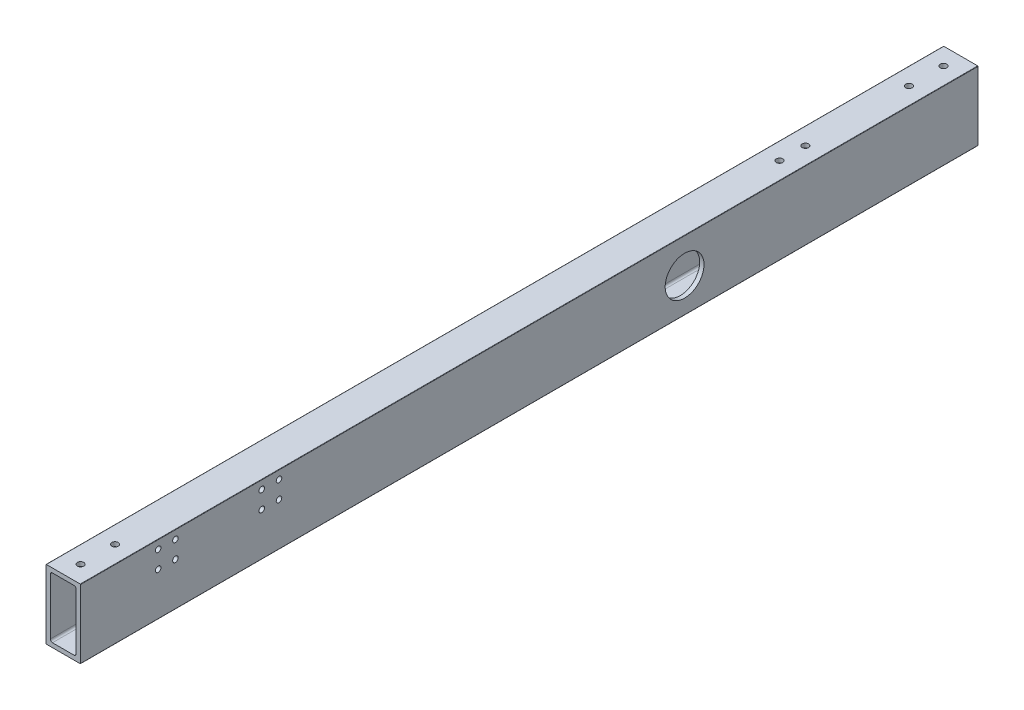
SolidWorks part; units mm, degrees
material "1060 Alloy"
ref_plane "Front Plane" through (0, 0, 0) normal (0, 0, 1) x (1, 0, 0)
ref_plane "Top Plane" through (0, 0, 0) normal (0, 1, 0) x (1, 0, 0)
ref_plane "Right Plane" through (0, 0, 0) normal (1, 0, 0) x (0, 0, -1)
ref_plane "Plane1" through (0, 0, 0) normal (0, 0, -1) x (-1, 0, 0)
sketch "Sketch1" plane through (0, 0, 0) normal (0, 0, -1) x (-1, 0, 0)
  line L0 (-3.175, 46.0375) -> (-3.175, 4.7625)
  line L1 (-4.7625, 3.175) -> (-20.6375, 3.175)
  line L2 (-22.225, 4.7625) -> (-22.225, 46.0375)
  line L3 (-20.6375, 47.625) -> (-4.7625, 47.625)
  line L4 (0, 0.254) -> (0, 50.546)
  line L5 (-0.254, 50.8) -> (-25.146, 50.8)
  line L6 (-25.4, 50.546) -> (-25.4, 0.254)
  line L7 (-25.146, 0) -> (-0.254, 0)
  arc A0 (-3.175, 4.7625) -> (-4.7625, 3.175) centre (-4.7625, 4.7625) cw
  arc A1 (-20.6375, 3.175) -> (-22.225, 4.7625) centre (-20.6375, 4.7625) cw
  arc A2 (-22.225, 46.0375) -> (-20.6375, 47.625) centre (-20.6375, 46.0375) cw
  arc A3 (-4.7625, 47.625) -> (-3.175, 46.0375) centre (-4.7625, 46.0375) cw
  arc A4 (-0.254, 0) -> (0, 0.254) centre (-0.254, 0.254) ccw
  arc A5 (0, 50.546) -> (-0.254, 50.8) centre (-0.254, 50.546) ccw
  arc A6 (-25.146, 50.8) -> (-25.4, 50.546) centre (-25.146, 50.546) ccw
  arc A7 (-25.4, 0.254) -> (-25.146, 0) centre (-25.146, 0.254) ccw
extrude "Boss-Extrude1" add sketch "Sketch1" against normal blind 660.4
sketch "Sketch2" plane through (0, 50.8, 0) normal (0, 1, 0) x (1, 0, 0)
  line L0 (0.254, -660.4) -> (25.146, -660.4) construction
  line L1 (25.146, -330.2) -> (0, -330.2) construction
  line L2 (25.146, -660.4) -> (25.146, 0) construction
  line L3 (0, -660.4) -> (0, 0) construction
  circle A0 centre (12.7, -647.7) radius 2.3813
  circle A1 centre (12.7, -622.3) radius 2.3813
  circle A2 centre (12.7, -38.1) radius 2.3812
  circle A3 centre (12.7, -12.7) radius 2.3813
  circle A4 centre (12.7, -133.35) radius 2.3813
  circle A5 centre (12.7, -114.3) radius 2.3813
  dimension "D1" = 4.7625
  dimension "D2" = 4.7625
  dimension "D3" = 12.7
  dimension "D4" = 25.4
  dimension "D6" = 4.7625
  dimension "D7" = 4.7625
  dimension "D5" = 76.2
  dimension "D8" = 19.05
extrude "Cut-Extrude1" cut sketch "Sketch2" against normal through all
sketch "Sketch5" plane through (25.4, 0, 0) normal (1, 0, 0) x (0, 0, -1)
  line L0 (-660.4, 50.546) -> (0, 50.546) construction
  line L2 (0, 50.546) -> (0, 0.254) construction
  circle A0 centre (-215.9, 25.146) radius 14.2875
  dimension "D1" = 28.575
  dimension "D2" = 25.4
  dimension "D3" = 215.9
extrude "Cut-Extrude2" cut sketch "Sketch5" against normal through all
sketch "Sketch7" plane through (0, 0, 0) normal (-1, 0, 0) x (0, 0, 1)
  circle A0 centre (514.35, 44.45) radius 2.032
  circle A1 centre (514.35, 31.75) radius 2.032
  circle A2 centre (527.05, 31.75) radius 2.032
  circle A3 centre (527.05, 44.45) radius 2.032
  circle A4 centre (590.55, 44.45) radius 2.032
  circle A5 centre (603.25, 44.45) radius 2.032
  circle A6 centre (603.25, 31.75) radius 2.032
  circle A7 centre (590.55, 31.75) radius 2.032
extrude "Cut-Extrude3" cut sketch "Sketch7" against normal through all both and the other way through all
